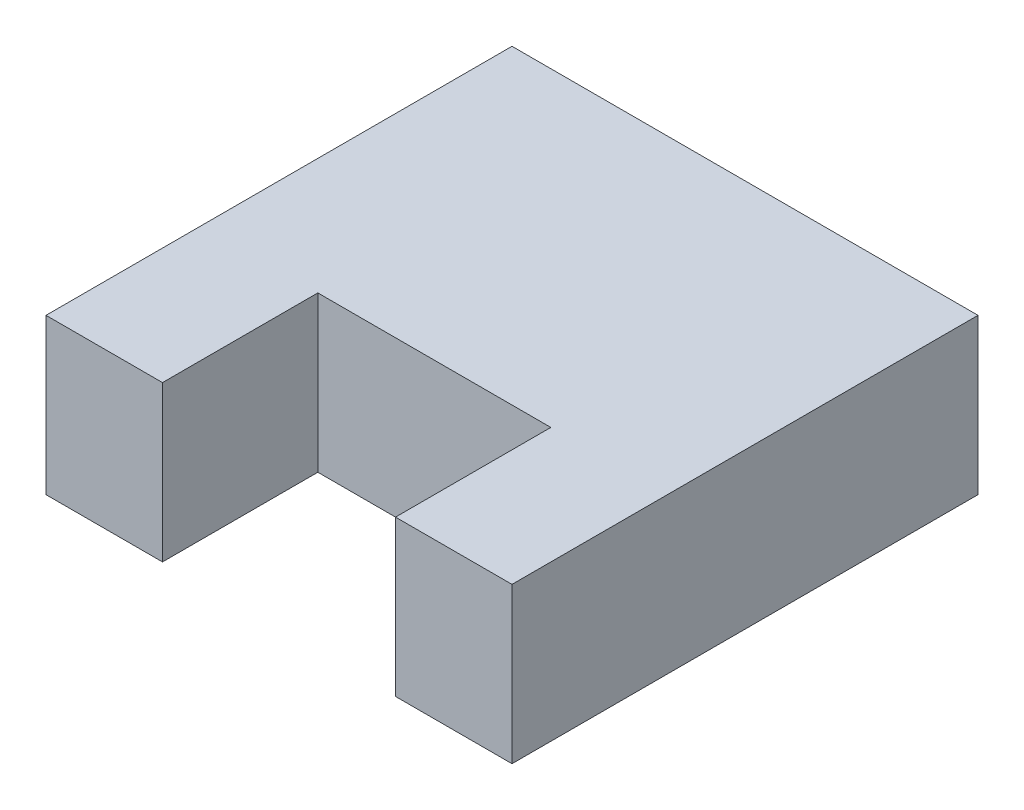
SolidWorks part; units mm, degrees
ref_plane "Front Plane" through (0, 0, 0) normal (0, 0, 1) x (1, 0, 0)
ref_plane "Top Plane" through (0, 0, 0) normal (0, 1, 0) x (1, 0, 0)
ref_plane "Right Plane" through (0, 0, 0) normal (1, 0, 0) x (0, 0, -1)
sketch "Sketch1" plane through (0, 0, 0) normal (0, 1, 0) x (1, 0, 0)
  line L0 (0, 0) -> (60, 0)
  line L1 (60, 0) -> (60, -60)
  line L2 (60, -60) -> (45, -60)
  line L3 (45, -60) -> (45, -40)
  line L4 (45, -40) -> (15, -40)
  line L5 (15, -40) -> (15, -60)
  line L6 (15, -60) -> (0, -60)
  line L7 (0, -60) -> (0, 0)
  dimension "D1" = 60
  dimension "D2" = 60
  dimension "D3" = 15
  dimension "D4" = 20
  dimension "D5" = 30
extrude "Boss-Extrude1" add sketch "Sketch1" along normal mid plane 20
